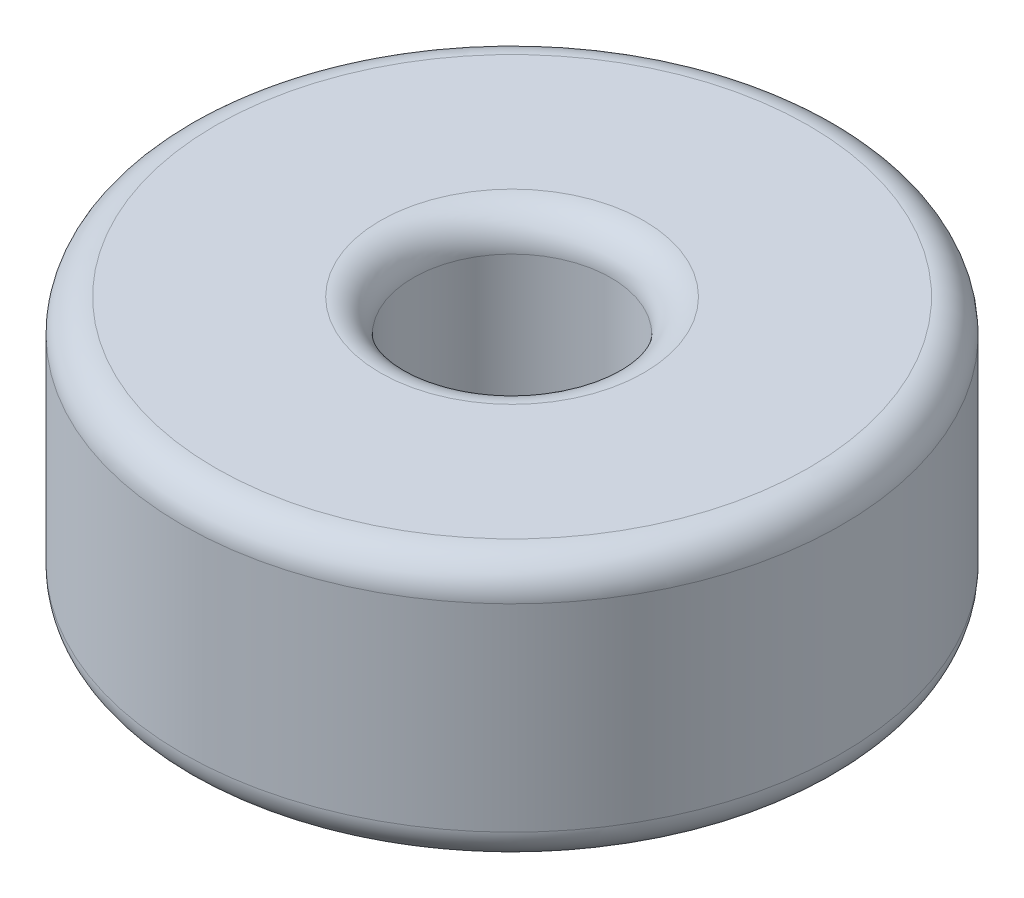
SolidWorks part; units mm, degrees
ref_plane "Front Plane" through (0, 0, 0) normal (0, 0, 1) x (1, 0, 0)
ref_plane "Top Plane" through (0, 0, 0) normal (0, 1, 0) x (1, 0, 0)
ref_plane "Right Plane" through (0, 0, 0) normal (1, 0, 0) x (0, 0, -1)
sketch "Sketch2" plane through (0, 0, 0) normal (0, 1, 0) x (1, 0, 0)
  circle A0 centre (0, 0) radius 1.5
  circle A1 centre (0, 0) radius 5
extrude "Boss-Extrude1" add sketch "Sketch2" along normal blind 4
fillet "Fillet1" radius 0.5 2 edges at (0, 4, 5) (0, 0, 5)
fillet "Fillet2" radius 0.5 2 edges at (0, 0, 1.5) (0, 4, 1.5)
